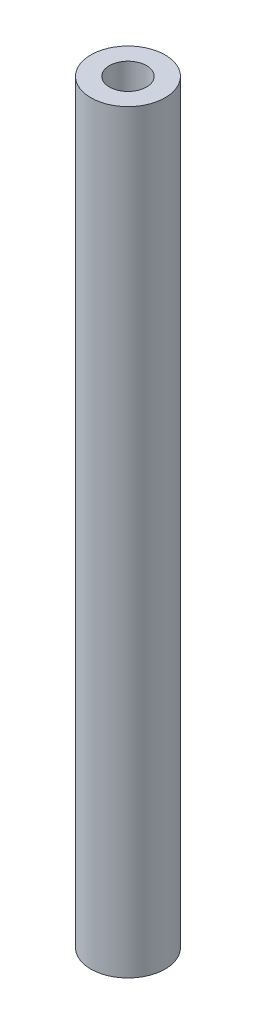
SolidWorks part; units mm, degrees
ref_plane "Front Plane" through (0, 0, 0) normal (0, 0, 1) x (1, 0, 0)
ref_plane "Top Plane" through (0, 0, 0) normal (0, 1, 0) x (1, 0, 0)
ref_plane "Right Plane" through (0, 0, 0) normal (1, 0, 0) x (0, 0, -1)
sketch "Sketch1" plane through (0, 0, 0) normal (0, 1, 0) x (1, 0, 0)
  circle A0 centre (0, 0) radius 5
extrude "Boss-Extrude1" add sketch "Sketch1" along normal blind 101.6 contours A0
hole_wizard "M6x1.0 Tapped Hole1" positions "Sketch2" profile "Sketch3" tap size "M6x1.0" standard "ANSI Metric" end condition through all
sketch "Sketch2" plane through (0, 0, 0) normal (0, -1, 0) x (-1, 0, 0)
  point P0 (0, 0)
sketch "Sketch3" plane through (0, 0, 0) normal (1, 0, 0) x (0, 0, -1)
  line L0 (0, 0) -> (0, 101.6)
  line L1 (0, 101.6) -> (2.5, 101.6)
  line L2 (2.5, 101.6) -> (2.5, 0.525)
  line L3 (2.5, 0.525) -> (3.025, 0)
  line L5 (3.025, 0) -> (0, 0)
  line L6 (-2.5, 0.525) -> (-3.025, 0) construction
  line L11 (0, -6.35) -> (0, 107.95) construction
  dimension "Thru Tap Drill Dia." = 5
  dimension "Thru Tap Drill Depth" = 101.6
  dimension "Near C'Sink Dia." = 6.05
  dimension "Near C'Sink Angle" = 90
cosmetic thread "Hole Thread1" parameters "D2"=6
